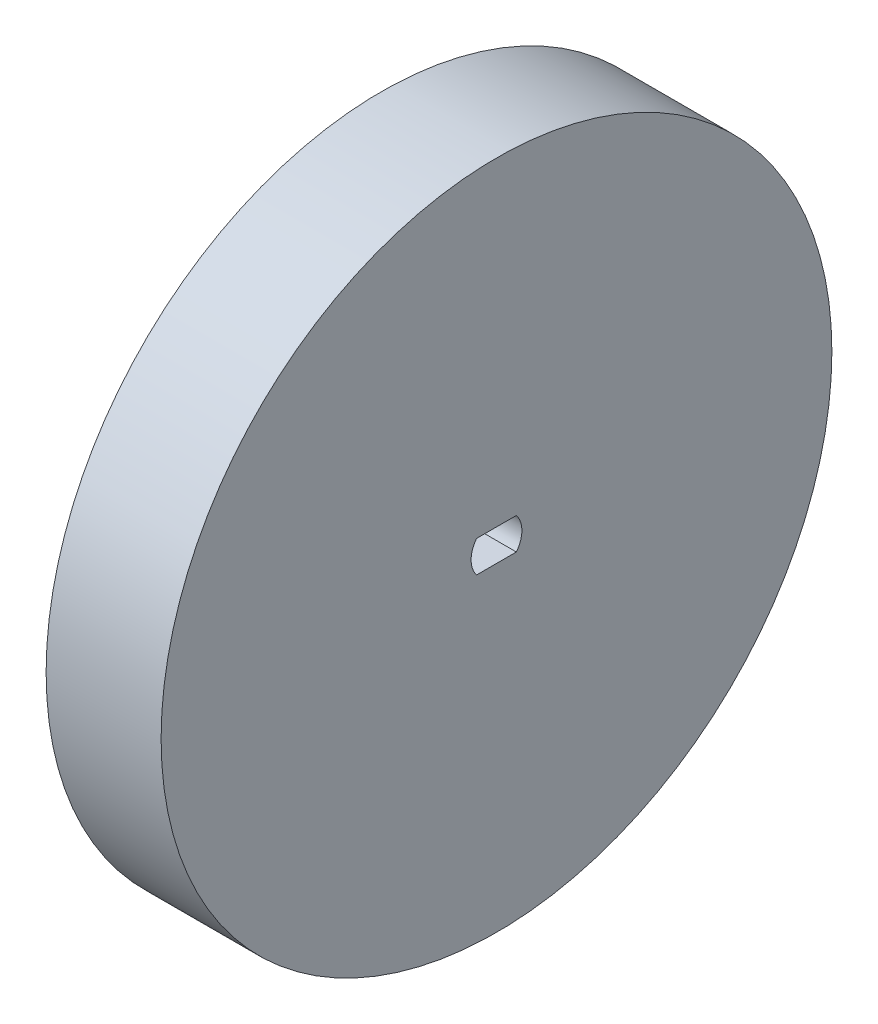
SolidWorks part; units mm, degrees
ref_plane "Front Plane" through (0, 0, 0) normal (0, 0, 1) x (1, 0, 0)
ref_plane "Top Plane" through (0, 0, 0) normal (0, 1, 0) x (1, 0, 0)
ref_plane "Right Plane" through (0, 0, 0) normal (1, 0, 0) x (0, 0, -1)
sketch "Sketch1" plane through (0, 0, 0) normal (1, 0, 0) x (0, 0, -1)
  line L0 (-2.0736, 1.65) -> (2.0736, 1.65)
  line L1 (-2.0736, -1.65) -> (2.0736, -1.65)
  circle A0 centre (0, 0) radius 35
  circle A1 centre (0, 0) radius 2.65
  dimension "D1" = 70
  dimension "D2" = 5.3
  dimension "D3" = 3.3
extrude "Boss-Extrude1" add sketch "Sketch1" against normal blind 12 contours A0 A1 | L0 A1 | L1 A1
